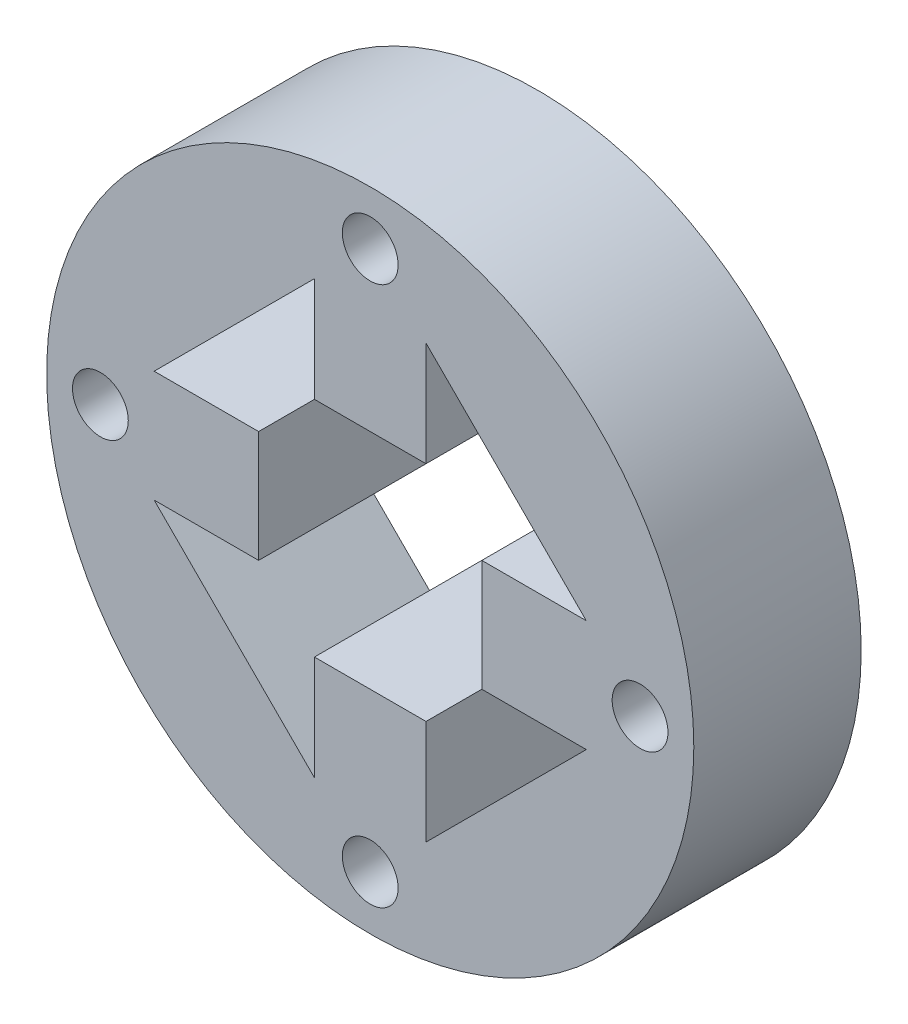
SolidWorks part; units mm, degrees
ref_plane "Front Plane" through (0, 0, 0) normal (0, 0, 1) x (1, 0, 0)
ref_plane "Top Plane" through (0, 0, 0) normal (0, 1, 0) x (1, 0, 0)
ref_plane "Right Plane" through (0, 0, 0) normal (1, 0, 0) x (0, 0, -1)
sketch "Sketch6" plane through (0, 0, 0) normal (0, 0, 1) x (1, 0, 0)
  circle A0 centre (0, 0) radius 20
  circle A1 centre (0, 0) radius 29
  dimension "D1" = 40
  dimension "D2" = 58
extrude "Inner Ring" add sketch "Sketch6" against normal blind 15 separate body
sketch "Sketch7" plane through (0, 0, 0) normal (0, 0, 1) x (1, 0, 0)
  line L2 (-10, 5) -> (-10, -5)
  line L3 (-5, 10) -> (5, 10)
  line L4 (10, 5) -> (10, -5)
  line L5 (-5, -10) -> (5, -10)
  line L14 (-19.3649, 5) -> (-10, 5)
  line L15 (-19.3649, -5) -> (-10, -5)
  line L16 (-5, 19.3649) -> (-5, 10)
  line L17 (5, 19.3649) -> (5, 10)
  line L18 (19.3649, 5) -> (10, 5)
  line L19 (19.3649, -5) -> (10, -5)
  line L20 (5, -19.3649) -> (5, -10)
  line L21 (-5, -19.3649) -> (-5, -10)
  circle A1 centre (0, 0) radius 20
  circle M19 centre (0, 0) radius 20
  dimension "D1" = 20
  dimension "D2" = 20
  dimension "D3" = 10
  dimension "D5" = 10
  dimension "D7" = 10
  dimension "D8" = 10
extrude "Motor Connector Cut" add sketch "Sketch7" against normal blind 15 contours L19 L18 L4 M19 | L17 L16 L3 M19 | L15 L2 L14 M19 | L21 L20 L5 M19
sketch "Sketch8" plane through (0, 0, 0) normal (0, 0, 1) x (1, 0, 0)
  circle A1 centre (0, 24.1825) radius 2.5
  circle A2 centre (24.1825, 0) radius 2.5
  circle A3 centre (0, -24.1825) radius 2.5
  circle A4 centre (-24.1825, 0) radius 2.5
  dimension "D1" = 5
  dimension "D2" = 5
  dimension "D3" = 5
  dimension "D4" = 5
  dimension "D6" = 48.3649
  dimension "D8" = 48.3649
extrude "M3 Holes" cut sketch "Sketch8" against normal blind 53 and the other way blind 38
sketch "Sketch9" plane through (0, 0, -15) normal (0, 0, -1) x (-1, 0, 0)
  line L0 (-19.3649, 5) -> (-5, 19.3649)
  line L2 (5, 19.3649) -> (19.3649, 5)
  line L4 (19.3649, -5) -> (5, -19.3649)
  line L6 (-5, -19.3649) -> (-19.3649, -5)
  arc A0 (-5, 19.3649) -> (-19.3649, 5) centre (0, 0) ccw
  arc A1 (5, -19.3649) -> (19.3649, -5) centre (0, 0) ccw
  arc A2 (-19.3649, -5) -> (-5, -19.3649) centre (0, 0) ccw
  arc A3 (19.3649, 5) -> (5, 19.3649) centre (0, 0) ccw
extrude "Boss-Extrude1" add sketch "Sketch9" against normal blind 15
